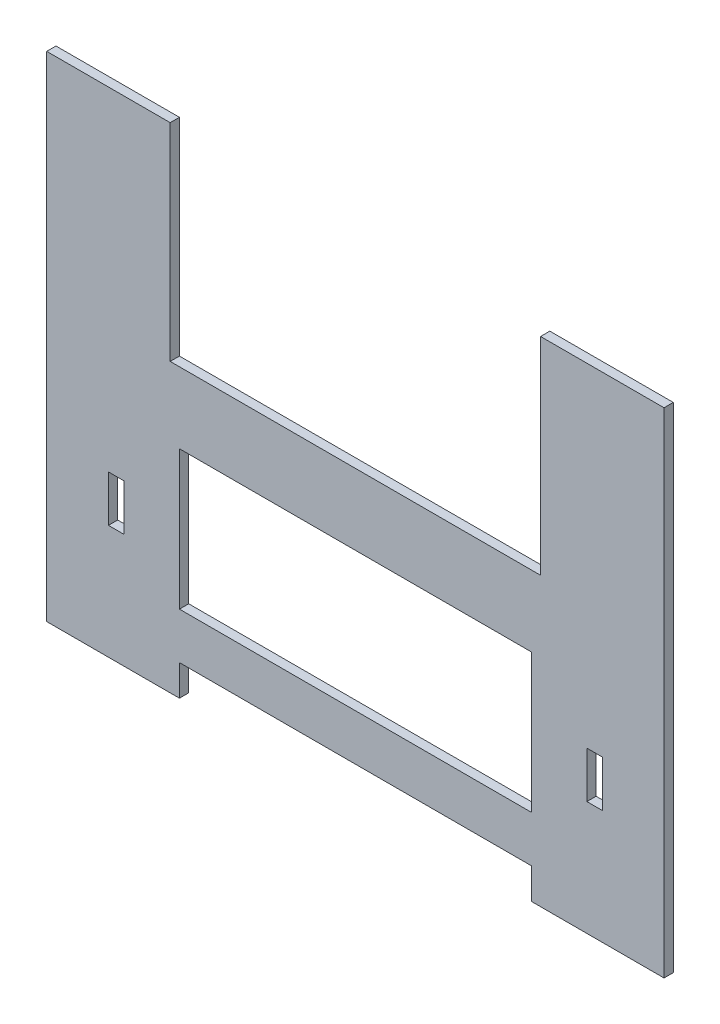
SolidWorks part; units mm, degrees
ref_plane "前视基准面" through (0, 0, 0) normal (0, 0, 1) x (1, 0, 0)
ref_plane "上视基准面" through (0, 0, 0) normal (0, 1, 0) x (1, 0, 0)
ref_plane "右视基准面" through (0, 0, 0) normal (1, 0, 0) x (0, 0, -1)
sketch "草图2" plane through (0, 0, 0) normal (0, 0, 1) x (1, 0, 0)
  line L0 (-57, -68) -> (-57, -23)
  line L1 (60, 67) -> (60, 0)
  line L2 (60, 0) -> (-60, 0)
  line L3 (60, 67) -> (100, 67)
  line L4 (100, 67) -> (100, -93)
  line L5 (100, -93) -> (57, -93)
  line L6 (57, -93) -> (57, -83)
  line L7 (57, -23) -> (-57, -23)
  line L8 (0, -102.843) -> (0, 102.843) construction
  line L9 (-57, -93) -> (-57, -83)
  line L10 (-100, -93) -> (-57, -93)
  line L11 (-100, 67) -> (-100, -93)
  line L12 (-60, 67) -> (-100, 67)
  line L13 (-60, 67) -> (-60, 0)
  line L14 (-57, -68) -> (57, -68)
  line L16 (-57, -83) -> (57, -83)
  line L18 (57, -68) -> (57, -23)
  point P12 (0, -23)
  point P13 (0, 0)
  dimension "D1" = 3
  dimension "D2" = 40
  dimension "D3" = 23
  dimension "D4" = 200
  dimension "D5" = 15
  dimension "D6" = 160
  dimension "D7" = 83
  dimension "D8" = 10
extrude "凸台-拉伸1" add sketch "草图2" along normal blind 3
sketch "草图3" plane through (0, 0, 3) normal (0, 0, 1) x (1, 0, 0)
  line L0 (-100, 67) -> (-100, -93) construction
  line L1 (-80, -41) -> (-75, -41)
  line L2 (-80, -41) -> (-80, -56)
  line L3 (-80, -56) -> (-75, -56)
  line L4 (-75, -41) -> (-75, -56)
  line L7 (-57, -68) -> (57, -68) construction
  line L8 (0, 0) -> (0, -83) construction
  line L9 (60, 0) -> (-60, 0) construction
  line L10 (-57, -83) -> (57, -83) construction
  line L11 (75, -41) -> (75, -56)
  line L12 (80, -56) -> (75, -56)
  line L13 (80, -41) -> (80, -56)
  line L14 (80, -41) -> (75, -41)
  dimension "D1" = 5
  dimension "D2" = 15
  dimension "D3" = 20
  dimension "D4" = 12
extrude "切除-拉伸1" cut sketch "草图3" against normal blind 10
